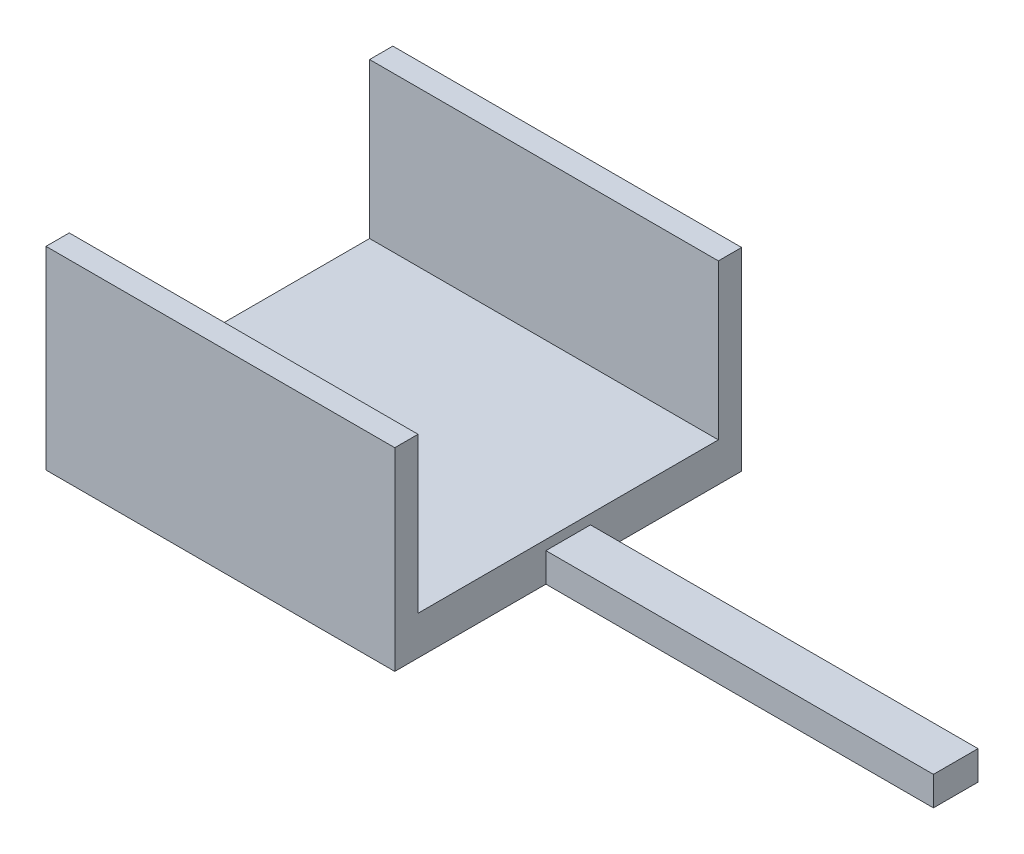
SolidWorks part; units mm, degrees
ref_plane "前视基准面" through (0, 0, 0) normal (0, 0, 1) x (1, 0, 0)
ref_plane "上视基准面" through (0, 0, 0) normal (0, 1, 0) x (1, 0, 0)
ref_plane "右视基准面" through (0, 0, 0) normal (1, 0, 0) x (0, 0, -1)
sketch "草图1" plane through (0, 0, 0) normal (0, 1, 0) x (1, 0, 0)
  line L0 (18, 10.1) -> (18, 17.9)
  line L1 (0, 0) -> (18, 0)
  line L2 (0, 0) -> (0, 17.9)
  line L3 (0, 17.9) -> (18, 17.9)
  line L4 (18, 0) -> (18, 7.8)
  line L5 (18, 7.8) -> (38, 7.8)
  line L7 (18, 10.1) -> (38, 10.1)
  line L8 (38, 7.8) -> (38, 10.1)
  dimension "D1" = 17.9
  dimension "D2" = 2.3
  dimension "D3" = 7.8
  dimension "D4" = 18
  dimension "D5" = 20
extrude "凸台-拉伸1" add sketch "草图1" along normal blind 1.5
sketch "草图2" plane through (0, 1.5, 0) normal (0, 1, 0) x (1, 0, 0)
  line L1 (0, 17.9) -> (18, 17.9)
  line L2 (0, 17.9) -> (0, 0)
  line L3 (0, 0) -> (18, 0)
  line L4 (18, 17.9) -> (18, 0)
extrude "凸台-拉伸2" add sketch "草图2" along normal blind 0.5
sketch "草图3" plane through (0, 2, 0) normal (0, 1, 0) x (1, 0, 0)
  line L0 (18, 0) -> (18, 17.9) construction
  line L1 (0, 17.9) -> (18, 17.9)
  line L2 (0, 17.9) -> (0, 16.7)
  line L3 (0, 16.7) -> (18, 16.7)
  line L4 (18, 17.9) -> (18, 16.7)
  line L6 (0, 0) -> (18, 0)
  line L7 (0, 0) -> (0, 1.2)
  line L8 (0, 1.2) -> (18, 1.2)
  line L9 (18, 0) -> (18, 1.2)
  dimension "D1" = 1.2
  dimension "D2" = 1.2
extrude "凸台-拉伸3" add sketch "草图3" along normal blind 8
